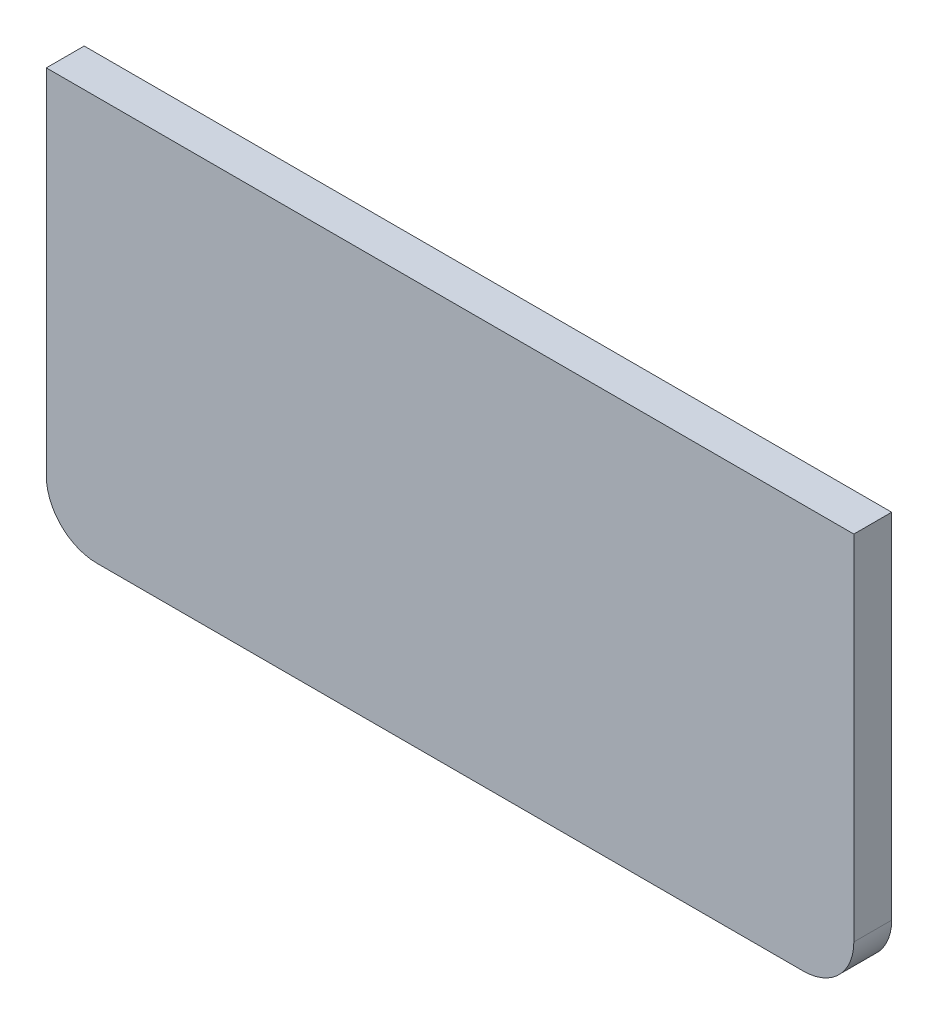
SolidWorks part; units mm, degrees
ref_plane "Front Plane" through (0, 0, 0) normal (0, 0, 1) x (1, 0, 0)
ref_plane "Top Plane" through (0, 0, 0) normal (0, 1, 0) x (1, 0, 0)
ref_plane "Right Plane" through (0, 0, 0) normal (1, 0, 0) x (0, 0, -1)
sketch "Sketch1" plane through (0, 0, 0) normal (0, 0, 1) x (1, 0, 0)
  line L1 (-101.6, 50.8) -> (101.6, 50.8)
  line L2 (-101.6, 50.8) -> (-101.6, -50.8)
  line L3 (-101.6, -50.8) -> (101.6, -50.8)
  line L4 (101.6, 50.8) -> (101.6, -50.8)
  line L5 (-101.6, 50.8) -> (101.6, -50.8) construction
  line L6 (-101.6, -50.8) -> (101.6, 50.8) construction
  point P0 (0, 0)
  dimension "D1" = 203.2
  dimension "D2" = 101.6
extrude "Boss-Extrude1" add sketch "Sketch1" along normal mid plane 9.525
fillet "Fillet1" radius 12.7 2 edges at (101.6, -50.8, 0) (-101.6, -50.8, 0)
sketch "Sketch2" plane through (0, 0, 4.7625) normal (0, 0, 1) x (1, 0, 0)
  line L0 (0, 50.8) -> (0, -50.8) construction
  line L1 (101.6, 50.8) -> (-101.6, 50.8) construction
  line L2 (-88.9, -50.8) -> (88.9, -50.8) construction
  line L3 (66.675, 50.8) -> (66.675, -50.8) construction
  line L4 (-66.675, 50.8) -> (-66.675, -50.8) construction
  dimension "D1" = 66.675
  dimension "D2" = 66.675
